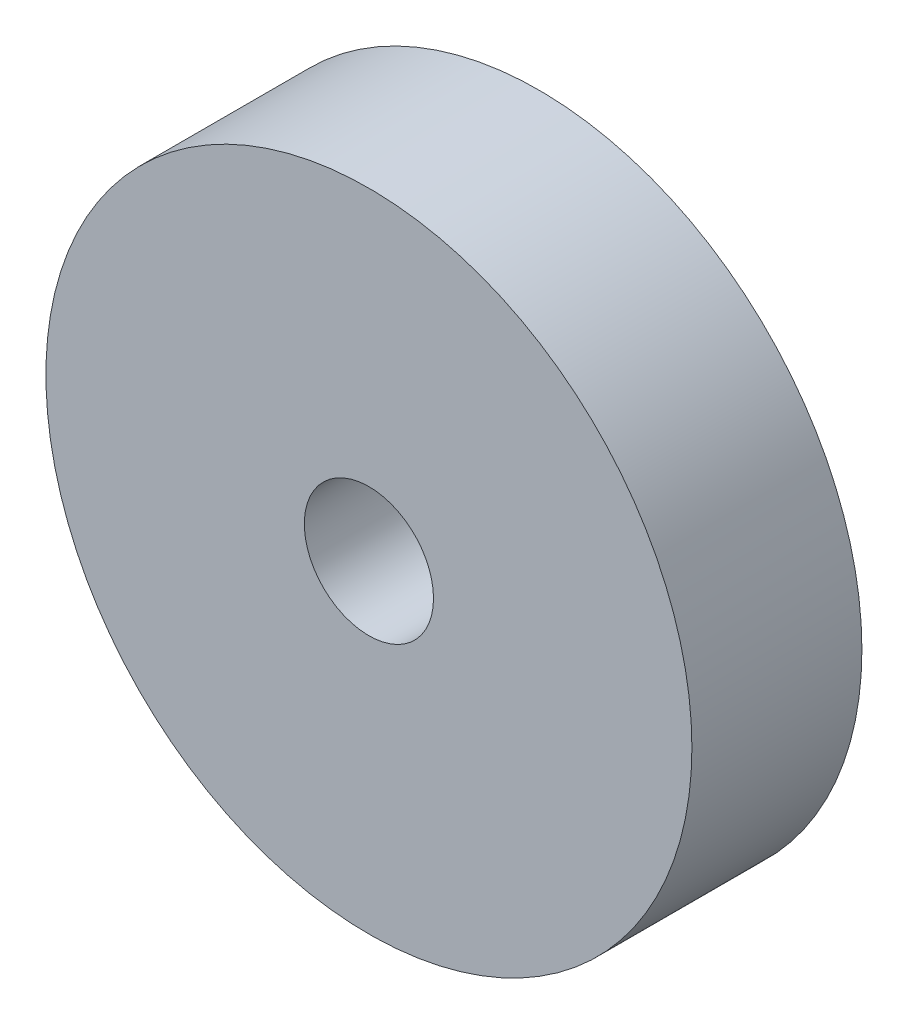
SolidWorks part; units mm, degrees
ref_plane "Front Plane" through (0, 0, 0) normal (0, 0, 1) x (1, 0, 0)
ref_plane "Top Plane" through (0, 0, 0) normal (0, 1, 0) x (1, 0, 0)
ref_plane "Right Plane" through (0, 0, 0) normal (1, 0, 0) x (0, 0, -1)
sketch "Sketch1" plane through (0, 0, 0) normal (0, 0, 1) x (1, 0, 0)
  circle A0 centre (0, 0) radius 95
  circle A1 centre (0, 0) radius 19
  dimension "D1" = 190
  dimension "D2" = 38
extrude "Boss-Extrude1" add sketch "Sketch1" along normal blind 50
